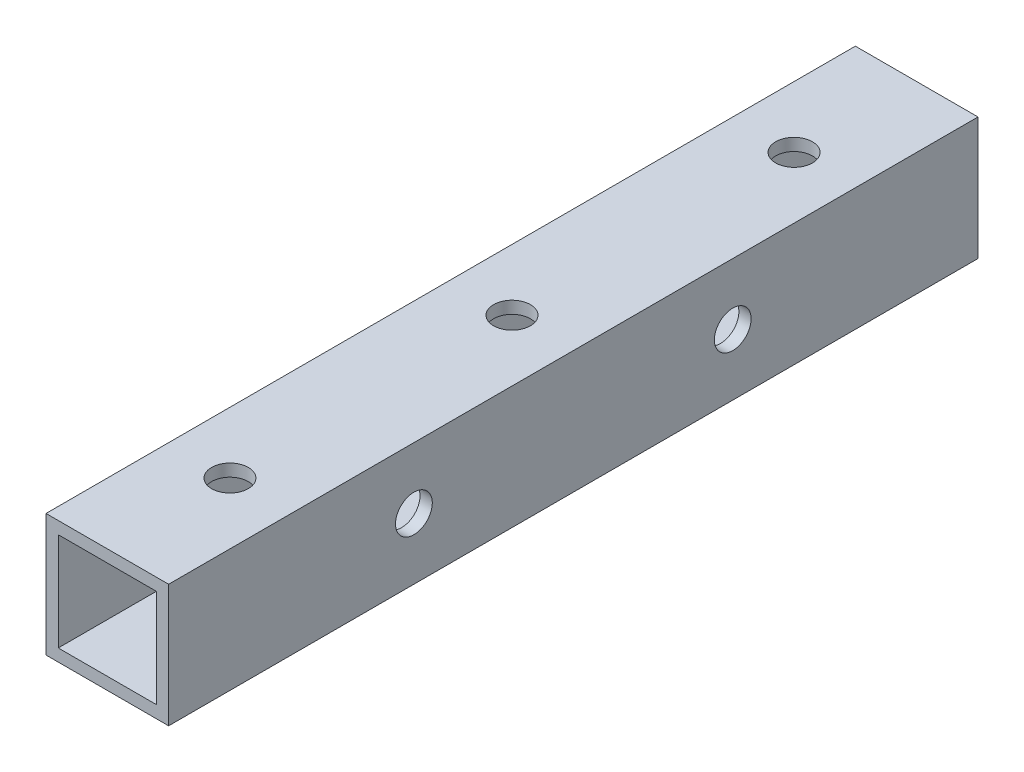
SolidWorks part; units mm, degrees
material "6063-O"
ref_plane "前视基准面" through (0, 0, 0) normal (0, 0, 1) x (1, 0, 0)
ref_plane "上视基准面" through (0, 0, 0) normal (0, 1, 0) x (1, 0, 0)
ref_plane "右视基准面" through (0, 0, 0) normal (1, 0, 0) x (0, 0, -1)
other "Configuration Table"
sketch "草图1" plane through (0, 0, 0) normal (0, 0, 1) x (1, 0, 0)
  line L1 (-58.1296, 118.347) -> (-68.1296, 118.347)
  line L2 (-58.1296, 118.347) -> (-58.1296, 108.347)
  line L3 (-58.1296, 108.347) -> (-68.1296, 108.347)
  line L4 (-68.1296, 118.347) -> (-68.1296, 108.347)
  line L5 (-58.1296, 118.347) -> (-68.1296, 108.347) construction
  line L6 (-58.1296, 108.347) -> (-68.1296, 118.347) construction
  point P4 (-63.1296, 113.347)
  dimension "D1" = 10
  dimension "D2" = 10
extrude "拉伸-薄壁1" add sketch "草图1" along normal blind 66 thin thin type one direction reverse wall 1
sketch "草图2" plane through (-58.1296, 0, 0) normal (1, 0, 0) x (0, 0, -1)
  line L0 (0, 113.347) -> (-66, 113.347) construction
  line L1 (0, 108.347) -> (0, 118.347) construction
  line L2 (-66, 108.347) -> (-66, 118.347) construction
  line L3 (-33, 108.347) -> (-33, 113.347) construction
  line L4 (-66, 108.347) -> (0, 108.347) construction
  circle A0 centre (-20, 113.347) radius 1.5
  circle A1 centre (-46, 113.347) radius 1.5
  dimension "D1" = 3
  dimension "D2" = 20
extrude "切除-拉伸1" cut sketch "草图2" against normal through all
sketch "草图3" plane through (0, 108.347, 0) normal (0, -1, 0) x (1, 0, 0)
  line L0 (-63.1296, 66) -> (-63.1296, 0) construction
  line L1 (-68.1296, 66) -> (-58.1296, 66) construction
  line L2 (-68.1296, 0) -> (-58.1296, 0) construction
  line L3 (-58.1296, 33) -> (-63.1296, 33) construction
  line L4 (-58.1296, 66) -> (-58.1296, 0) construction
  circle A1 centre (-63.1296, 10) radius 1.5
  circle A3 centre (-63.1296, 56) radius 1.5
  circle A4 centre (-63.1296, 33) radius 1.5
  dimension "D1" = 3
  dimension "D2" = 46
extrude "切除-拉伸2" cut sketch "草图3" against normal through all
